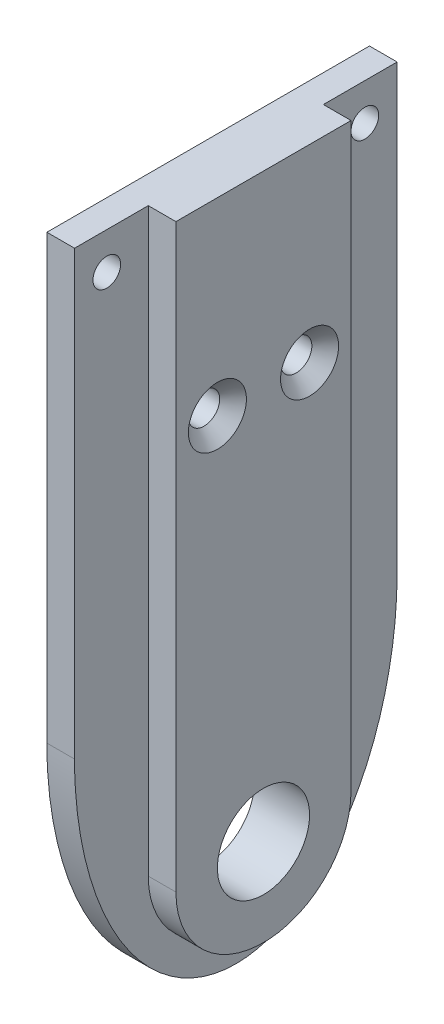
SolidWorks part; units mm, degrees
ref_plane "Front Plane" through (0, 0, 0) normal (0, 0, 1) x (1, 0, 0)
ref_plane "Top Plane" through (0, 0, 0) normal (0, 1, 0) x (1, 0, 0)
ref_plane "Right Plane" through (0, 0, 0) normal (1, 0, 0) x (0, 0, -1)
sketch "Sketch1" plane through (0, 0, 0) normal (1, 0, 0) x (0, 0, -1)
  line L0 (-17.5, 63) -> (-17.5, 0)
  line L1 (17.5, 0) -> (17.5, 63)
  line L2 (17.5, 63) -> (-17.5, 63)
  arc A0 (-17.5, 0) -> (17.5, 0) centre (0, 0) ccw
  dimension "D1" = 17.5
  dimension "D2" = 63
extrude "Boss-Extrude1" add sketch "Sketch1" along normal blind 6
sketch "Sketch5" plane through (6, 0, 0) normal (1, 0, 0) x (0, 0, -1)
  line L1 (17.5, 63) -> (-17.5, 63) construction
  line L2 (-9.5, 63) -> (-9.5, 0)
  line L3 (9.5, 0) -> (9.5, 63)
  line L5 (-9.5, 63) -> (-17.5, 63)
  line L8 (17.5, 63) -> (-17.5, 63)
  line L9 (-17.5, 63) -> (-17.5, 0)
  line L10 (17.5, 0) -> (17.5, 63)
  line L11 (17.5, 63) -> (9.5, 63)
  line L12 (-17.5, 63) -> (-17.5, 0)
  line L13 (17.5, 0) -> (17.5, 63)
  arc A0 (-9.5, 0) -> (9.5, 0) centre (0, 0) ccw
  arc A1 (-17.5, 0) -> (17.5, 0) centre (0, 0) ccw construction
  arc A3 (-17.5, 0) -> (17.5, 0) centre (0, 0) ccw
  arc A4 (-17.5, 0) -> (17.5, 0) centre (0, 0) ccw
  dimension "D1" = 9.5
  dimension "D2" = 0
extrude "Cut-Extrude1" cut sketch "Sketch5" against normal blind 3
hole_wizard "Ø3.0mm Dowel Hole1" positions "Sketch3" profile "Sketch4" hole size "Ø3.0" standard "ANSI Metric" end condition through all
sketch "Sketch3" plane through (3, 0, 0) normal (-1, 0, 0) x (0, 0, 1)
  line L0 (14, 59) -> (-14, 59) construction
  line L3 (0, 59) -> (0, 63) construction
  line L5 (-9.5, 63) -> (9.5, 63) construction
  point P0 (-14, 59)
  point P3 (14, 59)
  dimension "D1" = 4
  dimension "D2" = 28
sketch "Sketch4" plane through (3, 59, -14) normal (0, 1, 0) x (0, 0, -1)
  line L0 (0, 0) -> (0, 3)
  line L1 (0, 3) -> (1.5, 3)
  line L2 (1.5, 3) -> (1.5, 0)
  line L5 (1.5, 0) -> (0, 0)
  line L11 (0, -6.35) -> (0, 107.95) construction
  dimension "Thru Hole Dia." = 3
  dimension "Thru Hole Depth" = 3
sketch "Sketch6" plane through (3, 0, 0) normal (1, 0, 0) x (0, 0, -1)
  line L0 (17.5, 0) -> (17.5, 63) construction
  line L1 (-17.5, 63) -> (-17.5, 0) construction
  line L2 (-17.5, 15) -> (-17.5, 0)
  line L3 (17.5, 0) -> (17.5, 15)
  arc A0 (-17.5, 0) -> (17.5, 0) centre (0, 0) ccw construction
  arc A1 (-17.5, 0) -> (17.5, 0) centre (0, 0) ccw
  ellipse E0 centre (0, 15) end of major axis (0, 43) minor radius 17.5 (-17.5, 15) -> (17.5, 15) ccw
  dimension "D1" = 15
  dimension "D2" = 56
extrude "Cut-Extrude2" cut sketch "Sketch6" against normal up to surface (3 mm away) up to face at (0, 59, -15.5)
hole_wizard "CSK for M3 Flat Head Machine Screw1" positions "Sketch7" profile "Sketch8" countersink size "M3" standard "ANSI Metric" end condition through all
sketch "Sketch7" plane through (6, 0, 0) normal (1, 0, 0) x (0, 0, -1)
  line L0 (0, 0) -> (0, 63) construction
  line L1 (9.5, 63) -> (-9.5, 63) construction
  point P0 (-5, 42.5)
  point P2 (5, 42.5)
  dimension "D1" = 10
  dimension "D2" = 20.5
sketch "Sketch8" plane through (6, 42.5, 5) normal (0, 1, 0) x (0, 0, -1)
  line L0 (0, 0) -> (0, 6)
  line L1 (0, 6) -> (1.7, 6)
  line L2 (1.7, 6) -> (1.7, 1.45)
  line L3 (1.7, 1.45) -> (3.15, 0)
  line L5 (3.15, 0) -> (0, 0)
  line L6 (-1.7, 1.45) -> (-3.15, 0) construction
  line L11 (0, -6.35) -> (0, 107.95) construction
  dimension "Thru Hole Dia." = 3.4
  dimension "Thru Hole Depth" = 6
  dimension "Near C'Sink Dia." = 6.3
  dimension "Near C'Sink Angle" = 90
sketch "Sketch9" plane through (6, 0, 0) normal (1, 0, 0) x (0, 0, -1)
  circle A0 centre (0, 0) radius 5
  dimension "D1" = 10
extrude "Cut-Extrude3" cut sketch "Sketch9" against normal up to surface (6 mm away) up to face at (0, 42.5, 3.3)
